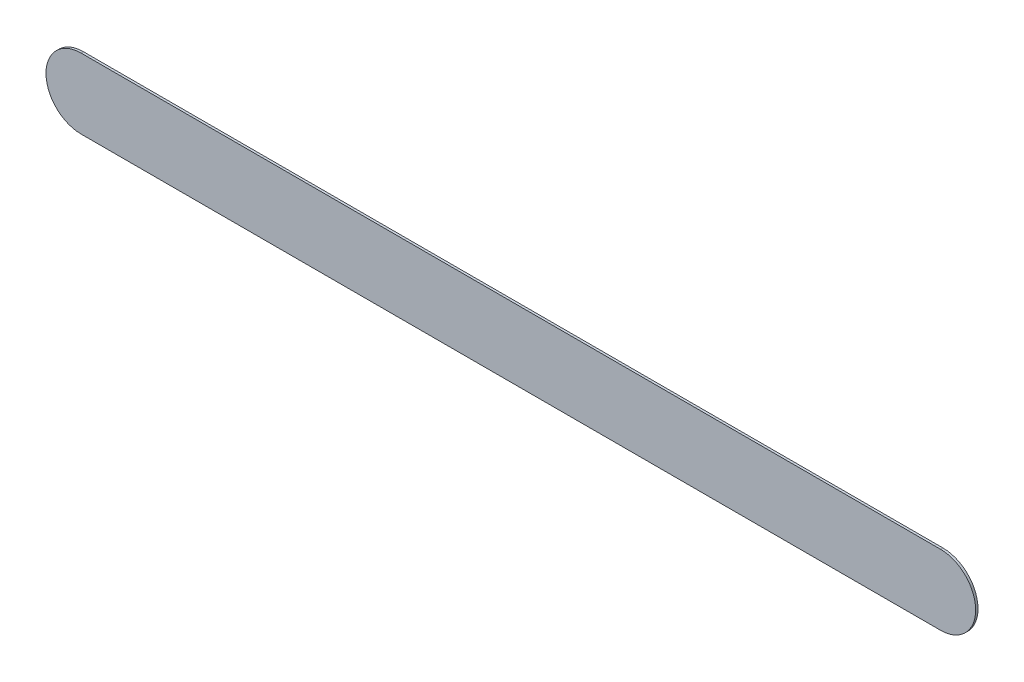
SolidWorks part; units mm, degrees
material "Custom Plastic"
ref_plane "Front Plane" through (0, 0, 0) normal (0, 0, 1) x (1, 0, 0)
ref_plane "Top Plane" through (0, 0, 0) normal (0, 1, 0) x (1, 0, 0)
ref_plane "Right Plane" through (0, 0, 0) normal (1, 0, 0) x (0, 0, -1)
sketch "Sketch1" plane through (0, 0, 0) normal (0, 0, 1) x (1, 0, 0)
  line L0 (-356.506, 0) -> (743.294, 0) construction
  line L1 (-356.506, 44.9) -> (743.294, 44.9)
  line L2 (-356.506, -44.9) -> (743.294, -44.9)
  arc A0 (-356.506, 44.9) -> (-356.506, -44.9) centre (-356.506, 0) ccw
  arc A1 (743.294, -44.9) -> (743.294, 44.9) centre (743.294, 0) ccw
  point P3 (193.394, 0)
  dimension "D1" = 44.9
  dimension "D2" = 1099.8
extrude "Boss-Extrude2" add sketch "Sketch1" along normal blind 3 contours L2 A1 L1 A0
